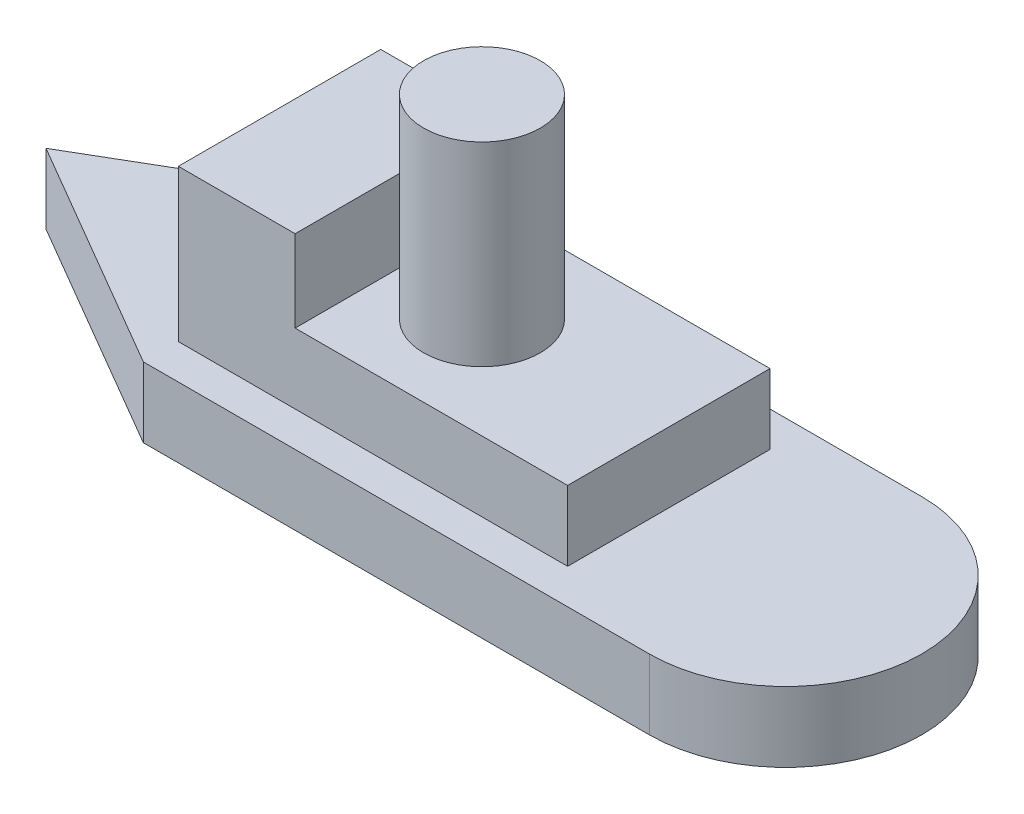
SolidWorks part; units mm, degrees
ref_plane "Front Plane" through (0, 0, 0) normal (0, 0, 1) x (1, 0, 0)
ref_plane "HP" through (0, 0, 0) normal (0, 1, 0) x (1, 0, 0)
ref_plane "Right Plane" through (0, 0, 0) normal (1, 0, 0) x (0, 0, -1)
sketch "Sketch1" plane through (0, 0, 0) normal (0, 1, 0) x (1, 0, 0)
  line L0 (0, 0) -> (60, 35)
  line L1 (190, 35) -> (60, 35)
  line L2 (0, 0) -> (225, 0) construction
  line L3 (190, -35) -> (60, -35)
  line L4 (0, 0) -> (60, -35)
  arc A0 (190, 35) -> (190, -35) centre (190, 0) cw
  dimension "D2" = 35
  dimension "D1" = 225
  dimension "D3" = 130
  dimension "D4" = 60
extrude "Boss-Extrude1" add sketch "Sketch1" along normal blind 18
sketch "Sketch2" plane through (0, 18, 0) normal (0, 1, 0) x (1, 0, 0)
  line L0 (190, 35) -> (60, 35) construction
  line L1 (60, 26) -> (160, 26)
  line L2 (60, 26) -> (60, -26)
  line L3 (60, -26) -> (160, -26)
  line L4 (160, 26) -> (160, -26)
  dimension "D1" = 100
  dimension "D2" = 52
  dimension "D3" = 9
  dimension "D4" = 60
extrude "Boss-Extrude2" add sketch "Sketch2" along normal blind 18
sketch "Sketch3" plane through (0, 36, 0) normal (0, 1, 0) x (1, 0, 0)
  line L0 (60, -26) -> (160, -26) construction
  line L1 (60, 26) -> (90, 26)
  line L2 (60, 26) -> (60, -26)
  line L3 (60, -26) -> (90, -26)
  line L4 (90, 26) -> (90, -26)
  dimension "D1" = 30
extrude "Boss-Extrude3" add sketch "Sketch3" along normal blind 21
sketch "Sketch4" plane through (0, 36, 0) normal (0, 1, 0) x (1, 0, 0)
  line L0 (90, -26) -> (90, 26) construction
  line L1 (90, -26) -> (160, -26) construction
  circle A0 centre (112, 0) radius 15
  dimension "D1" = 30
  dimension "D2" = 22
  dimension "D3" = 26
extrude "Boss-Extrude4" add sketch "Sketch4" along normal blind 50
equation "\"D2@Sketch2\"=70-18"
